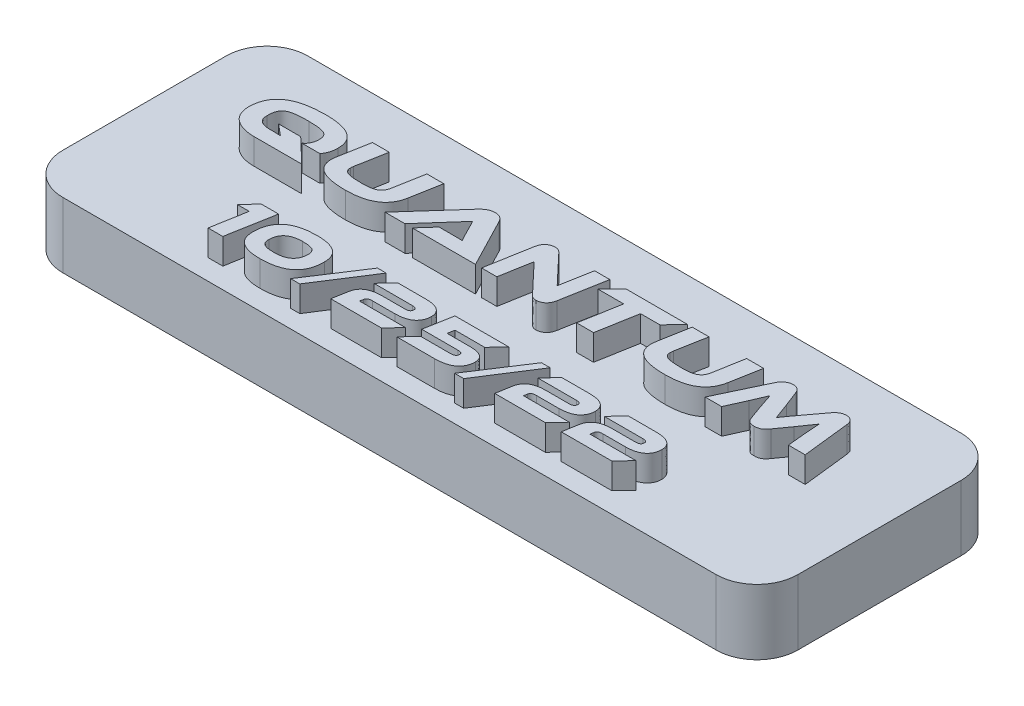
SolidWorks part; units mm, degrees
ref_plane "Front Plane" through (0, 0, 0) normal (0, 0, 1) x (1, 0, 0)
ref_plane "Top Plane" through (0, 0, 0) normal (0, 1, 0) x (1, 0, 0)
ref_plane "Right Plane" through (0, 0, 0) normal (1, 0, 0) x (0, 0, -1)
sketch "Sketch1" plane through (0, 0, 0) normal (0, 1, 0) x (1, 0, 0)
  line L1 (-28.575, 9.525) -> (28.575, 9.525)
  line L2 (-28.575, 9.525) -> (-28.575, -9.525)
  line L3 (-28.575, -9.525) -> (28.575, -9.525)
  line L4 (28.575, 9.525) -> (28.575, -9.525)
  line L5 (-28.575, 9.525) -> (28.575, -9.525) construction
  line L6 (-28.575, -9.525) -> (28.575, 9.525) construction
  point P0 (0, 0)
  dimension "D1" = 57.15
  dimension "D2" = 19.05
extrude "Boss-Extrude1" add sketch "Sketch1" along normal up to surface (5.08 mm away)
fillet "Fillet1" radius 3.175 4 edges at (-28.575, 2.54, 9.525) (-28.575, 2.54, -9.525) (28.575, 2.54, 9.525) (28.575, 2.54, -9.525)
sketch "Sketch3" plane through (0, 5.08, 0) normal (0, 1, 0) x (1, 0, 0)
  line L0 (28.575, -7.9375) -> (-28.575, -7.9375) construction
  line L1 (28.575, -6.35) -> (28.575, 6.35) construction
  line L2 (-28.575, 6.35) -> (-28.575, -6.35) construction
  line L3 (28.575, 0) -> (-28.575, 0) construction
  line L5 (-25.4, -9.525) -> (25.4, -9.525) construction
  line L6 (25.4, 9.525) -> (-25.4, 9.525) construction
  text T0 "quantum\r\n" font "Ethnocentric Rg" height in points 16
  text T1 "10/25/22\r\n" font "Ethnocentric Rg" height in points 14
  point P8 (-28.575, 0)
  dimension "D1" = 1.5875
extrude "Boss-Extrude2" add sketch "Sketch3" along normal blind 2
sketch "Sketch4" plane through (0, 0, 0) normal (0, -1, 0) x (1, 0, 0)
  line L0 (25.4, 0) -> (-25.4, 0) construction
  circle A0 centre (-25.4, 0) radius 0.9
  circle A1 centre (25.4, 0) radius 0.9
  point P3 (0, 0)
  dimension "D2" = 1.8
  dimension "D1" = 50.8
extrude "Cut-Extrude1" cut sketch "Sketch4" against normal blind 4
